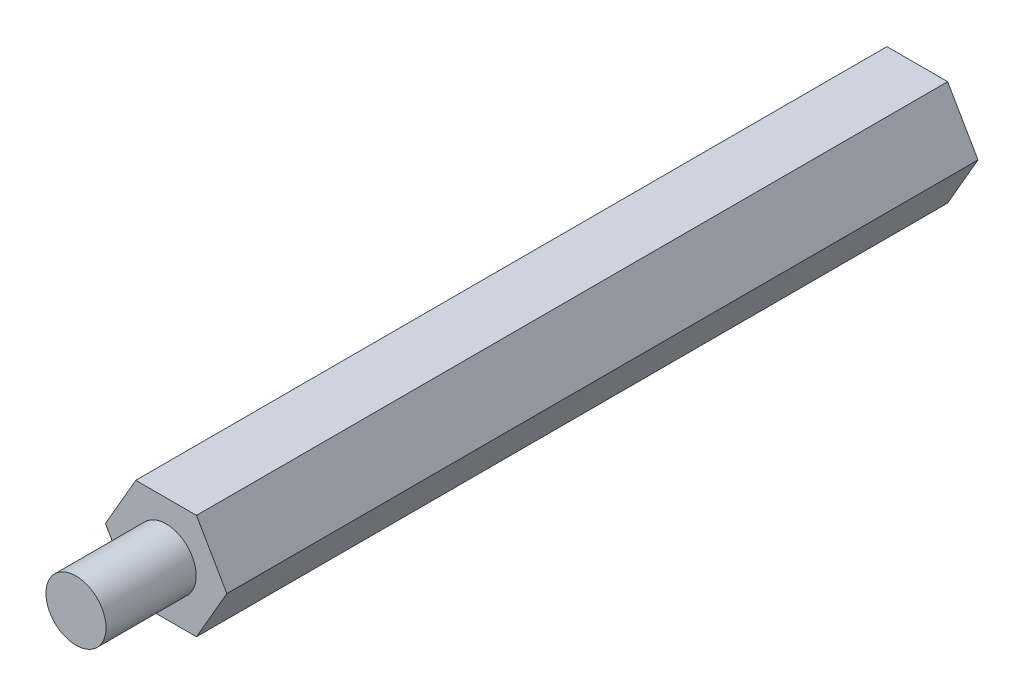
SolidWorks part; units mm, degrees
material "黃銅"
ref_plane "前基準面" through (0, 0, 0) normal (0, 0, 1) x (1, 0, 0)
ref_plane "上基準面" through (0, 0, 0) normal (0, 1, 0) x (1, 0, 0)
ref_plane "右基準面" through (0, 0, 0) normal (1, 0, 0) x (0, 0, -1)
sketch "草圖1" plane through (0, 0, 0) normal (0, 0, 1) x (1, 0, 0)
  line L1 (4.0415, 0) -> (2.0207, 3.5)
  line L2 (2.0207, 3.5) -> (-2.0207, 3.5)
  line L3 (-2.0207, 3.5) -> (-4.0415, 0)
  line L4 (-4.0415, 0) -> (-2.0207, -3.5)
  line L5 (-2.0207, -3.5) -> (2.0207, -3.5)
  line L6 (2.0207, -3.5) -> (4.0415, 0)
  circle A0 centre (0, 0) radius 3.5 construction
  dimension "D1" = 7
extrude "填料-伸長1" add sketch "草圖1" along normal blind 50
sketch "草圖2" plane through (0, 0, 50) normal (0, 0, 1) x (1, 0, 0)
  circle A0 centre (0, 0) radius 2
  dimension "D1" = 4
extrude "填料-伸長2" add sketch "草圖2" along normal blind 6
hole_wizard "M4x0.7 螺紋孔1" positions "草圖3" profile "草圖4" tap size "M4x0.7" standard "Ansi Metric"
sketch "草圖3" plane through (0, 0, 0) normal (0, 0, -1) x (-1, 0, 0)
  point P0 (0, 0)
sketch "草圖4" plane through (0, 0, 0) normal (1, 0, 0) x (0, 1, 0)
  line L0 (0, 0) -> (0, 11.4914)
  line L1 (0, 11.4914) -> (1.65, 10.5)
  line L2 (1.65, 10.5) -> (1.65, 0)
  line L5 (1.65, 0) -> (0, 0)
  line L10 (0, 11.4914) -> (-1.65, 10.5) construction
  line L11 (0, -6.35) -> (0, 107.95) construction
  dimension "螺孔鑽直徑" = 3.3
  dimension "螺孔鑽深度" = 10.5
  dimension "導頭角度" = 118
cosmetic thread "鑽孔螺紋1" parameters "D1"=8, "D2"=4
